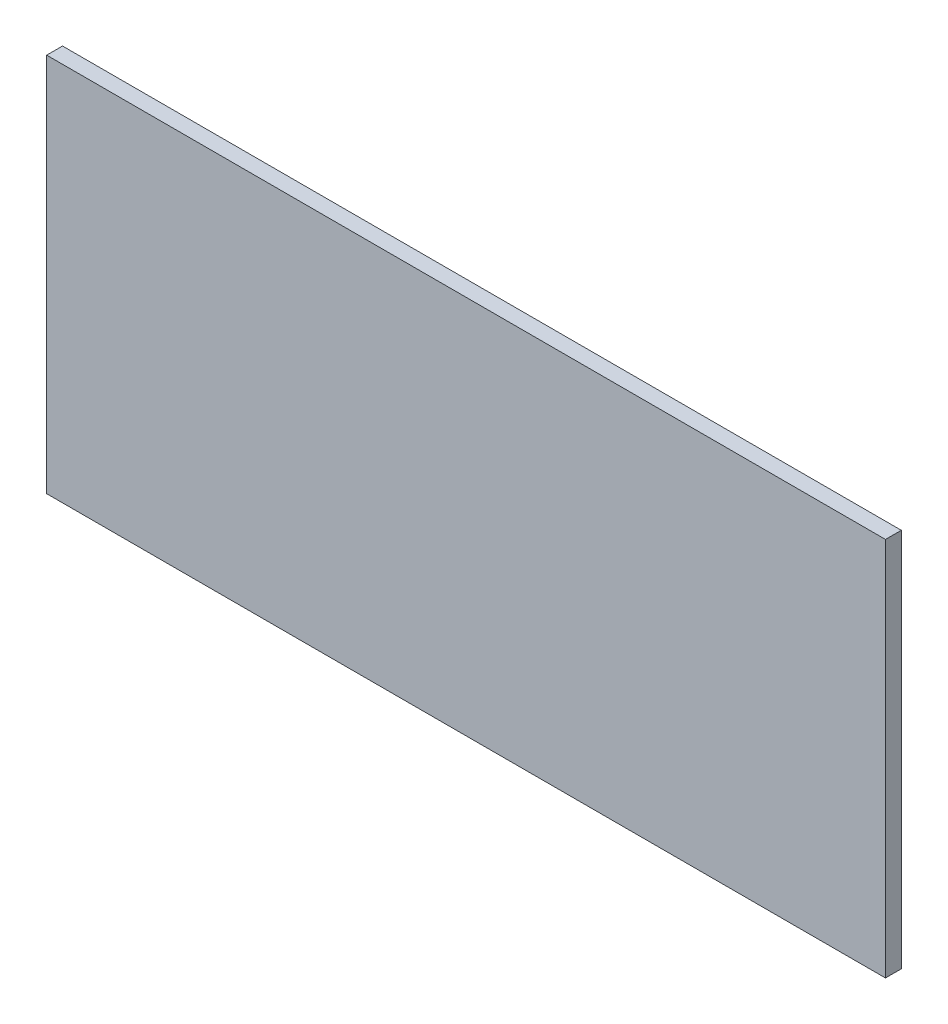
SolidWorks part; units mm, degrees
ref_plane "Ön Düzlem" through (0, 0, 0) normal (0, 0, 1) x (1, 0, 0)
ref_plane "Üst Düzlem" through (0, 0, 0) normal (0, 1, 0) x (1, 0, 0)
ref_plane "Sağ Düzlem" through (0, 0, 0) normal (1, 0, 0) x (0, 0, -1)
sketch "Sketch1" plane through (0, 0, 0) normal (0, 0, 1) x (1, 0, 0)
  line L1 (-265, -120) -> (265, -120)
  line L2 (-265, -120) -> (-265, 120)
  line L3 (-265, 120) -> (265, 120)
  line L4 (265, -120) -> (265, 120)
  line L5 (-265, -120) -> (265, 120) construction
  line L6 (-265, 120) -> (265, -120) construction
  point P0 (0, 0)
  dimension "D1" = 530
  dimension "D2" = 240
extrude "Boss-Extrude1" add sketch "Sketch1" along normal blind 10 contours L2 L3 L4 L1
